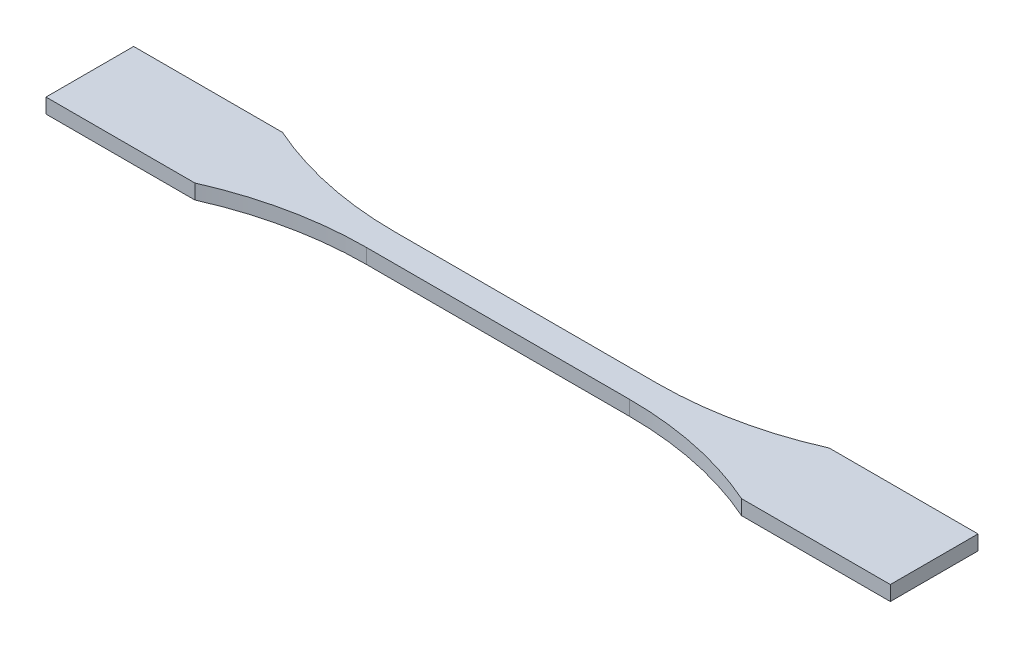
SolidWorks part; units mm, degrees
material "PET"
ref_plane "Alzado" through (0, 0, 0) normal (0, 0, 1) x (1, 0, 0)
ref_plane "Planta" through (0, 0, 0) normal (0, 1, 0) x (1, 0, 0)
ref_plane "Vista lateral" through (0, 0, 0) normal (1, 0, 0) x (0, 0, -1)
sketch "Croquis1" plane through (0, 0, 0) normal (0, 1, 0) x (1, 0, 0)
  line L1 (91.5, -9.5) -> (-91.5, -9.5)
  line L2 (91.5, -9.5) -> (91.5, 9.5)
  line L3 (91.5, 9.5) -> (-91.5, 9.5)
  line L4 (-91.5, -9.5) -> (-91.5, 9.5)
  line L5 (91.5, -9.5) -> (-91.5, 9.5) construction
  line L6 (91.5, 9.5) -> (-91.5, -9.5) construction
  line L7 (28.5, -3) -> (-28.5, -3)
  line L8 (28.5, -3) -> (28.5, 3)
  line L9 (28.5, 3) -> (-28.5, 3)
  line L10 (-28.5, -3) -> (-28.5, 3)
  line L11 (28.5, -3) -> (-28.5, 3) construction
  line L12 (28.5, 3) -> (-28.5, -3) construction
  arc A0 (-59.253, 9.5) -> (-28.5, 3) centre (-28.5, 79) ccw
  arc A3 (59.253, -9.5) -> (28.5, -3) centre (28.5, -79) ccw
  arc A4 (28.5, 3) -> (59.253, 9.5) centre (28.5, 79) ccw
  arc A6 (-28.5, -3) -> (-59.253, -9.5) centre (-28.5, -79) ccw
  point P0 (0, 0)
  point P6 (0, 0)
  dimension "D5" = 152
  dimension "D1" = 19
  dimension "D2" = 183
  dimension "D3" = 6
  dimension "D4" = 57
extrude "Saliente-Extruir1" add sketch "Croquis1" along normal mid plane 3.2 contours A6 L10 A0 L3 L4 L1 | A4 L8 A3 L1 L2 L3 | L10 L7 L8 L9
sketch "Croquis2" plane through (0, 1.6, 0) normal (0, 1, 0) x (1, 0, 0)
  line L0 (-67.5, 9.5) -> (-67.5, -9.5)
  line L1 (-59.253, 9.5) -> (-91.5, 9.5) construction
  line L2 (-59.253, -9.5) -> (-91.5, -9.5) construction
  line L3 (67.5, 9.5) -> (67.5, -9.5)
  line L4 (91.5, 9.5) -> (59.253, 9.5) construction
  line L5 (91.5, -9.5) -> (59.253, -9.5) construction
  line L6 (67.5, 0) -> (-67.5, 0) construction
  point P14 (0, 0)
  dimension "D1" = 135
